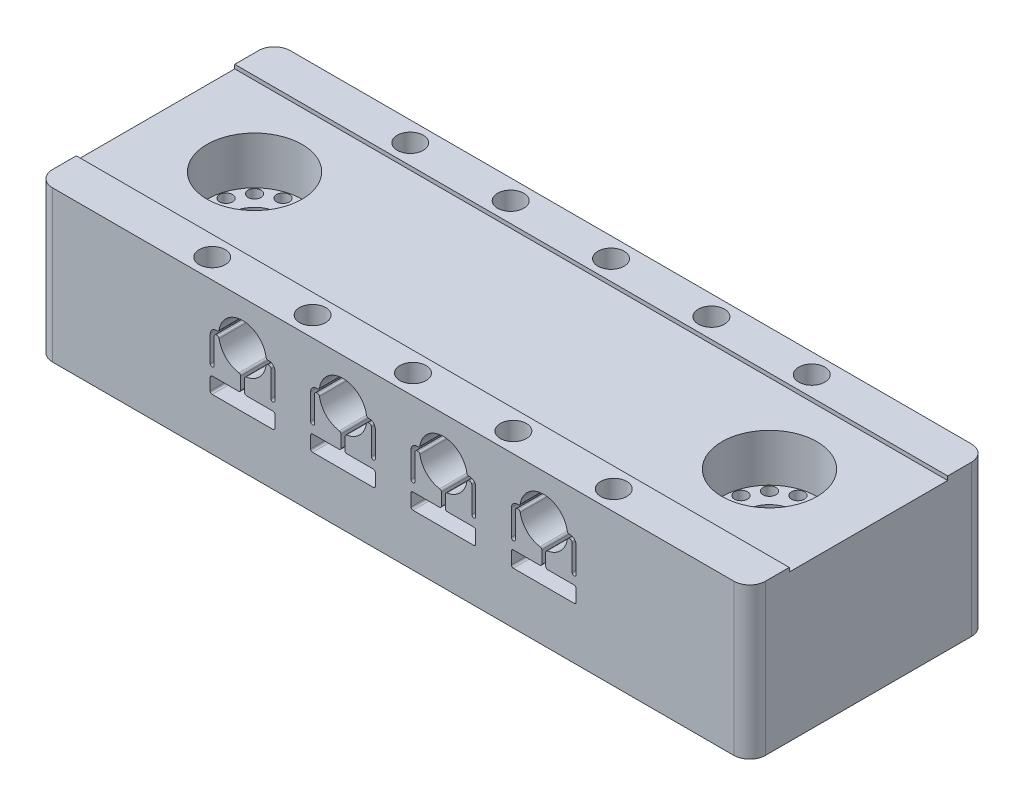
SolidWorks part; units mm, degrees
ref_plane "Front Plane" through (0, 0, 0) normal (0, 0, 1) x (1, 0, 0)
ref_plane "Top Plane" through (0, 0, 0) normal (0, 1, 0) x (1, 0, 0)
ref_plane "Right Plane" through (0, 0, 0) normal (1, 0, 0) x (0, 0, -1)
sketch "Sketch1" plane through (0, 0, 0) normal (0, 1, 0) x (1, 0, 0)
  line L0 (-45, 13) -> (-45, -13)
  line L3 (-43, -15) -> (43, -15)
  line L4 (45, -13) -> (45, 13)
  line L5 (43, 15) -> (-43, 15)
  line L6 (-32.5, 0) -> (32.5, 0) construction
  line L8 (-33.8159, 4.9109) -> (-36.095, 3.595) construction
  line L9 (-36.095, 3.595) -> (-37.4109, 1.3159) construction
  line L10 (-37.4109, 1.3159) -> (-37.4109, -1.3159) construction
  line L11 (-37.4109, -1.3159) -> (-36.095, -3.595) construction
  line L12 (-36.095, -3.595) -> (-33.8159, -4.9109) construction
  line L13 (-33.8159, -4.9109) -> (-31.1841, -4.9109) construction
  line L14 (-31.1841, -4.9109) -> (-28.905, -3.595) construction
  line L15 (-28.905, -3.595) -> (-27.5891, -1.3159) construction
  line L16 (-27.5891, -1.3159) -> (-27.5891, 1.3159) construction
  line L17 (-27.5891, 1.3159) -> (-28.905, 3.595) construction
  line L18 (-28.905, 3.595) -> (-31.1841, 4.9109) construction
  line L19 (-31.1841, 4.9109) -> (-33.8159, 4.9109) construction
  line L20 (33.8159, 4.9109) -> (31.1841, 4.9109) construction
  line L21 (31.1841, 4.9109) -> (28.905, 3.595) construction
  line L22 (28.905, 3.595) -> (27.5891, 1.3159) construction
  line L23 (27.5891, 1.3159) -> (27.5891, -1.3159) construction
  line L24 (27.5891, -1.3159) -> (28.905, -3.595) construction
  line L25 (28.905, -3.595) -> (31.1841, -4.9109) construction
  line L26 (31.1841, -4.9109) -> (33.8159, -4.9109) construction
  line L27 (33.8159, -4.9109) -> (36.095, -3.595) construction
  line L28 (36.095, -3.595) -> (37.4109, -1.3159) construction
  line L29 (37.4109, -1.3159) -> (37.4109, 1.3159) construction
  line L30 (37.4109, 1.3159) -> (36.095, 3.595) construction
  line L31 (36.095, 3.595) -> (33.8159, 4.9109) construction
  circle A2 centre (-32.5, 0) radius 3
  circle A3 centre (32.5, 0) radius 3
  circle A17 centre (32.5, 0) radius 6 construction
  circle A18 centre (-32.5, 0) radius 6 construction
  circle A19 centre (-31.1841, 4.9109) radius 0.9159 construction
  circle A20 centre (-31.1841, 4.9109) radius 0.8159
  circle A21 centre (-32.5, 0) radius 4.9109 construction
  circle A22 centre (-33.8159, 4.9109) radius 0.8159
  circle A23 centre (-33.8159, 4.9109) radius 1.8159 construction
  circle A24 centre (-36.095, 3.595) radius 0.8159
  circle A25 centre (-37.4109, 1.3159) radius 0.8159
  circle A26 centre (-37.4109, -1.3159) radius 0.8159
  circle A27 centre (-36.095, -3.595) radius 0.8159
  circle A28 centre (-33.8159, -4.9109) radius 0.8159
  circle A29 centre (-31.1841, -4.9109) radius 0.8159
  circle A30 centre (-28.905, -3.595) radius 0.8159
  circle A31 centre (-27.5891, -1.3159) radius 0.8159
  circle A32 centre (-27.5891, 1.3159) radius 0.8159
  circle A33 centre (-28.905, 3.595) radius 0.8159
  circle A34 centre (32.5, 0) radius 4.9109 construction
  circle A35 centre (31.1841, 4.9109) radius 0.8159
  circle A36 centre (33.8159, 4.9109) radius 0.8159
  circle A37 centre (36.095, 3.595) radius 0.8159
  circle A38 centre (37.4109, 1.3159) radius 0.8159
  circle A39 centre (37.4109, -1.3159) radius 0.8159
  circle A40 centre (36.095, -3.595) radius 0.8159
  circle A41 centre (33.8159, -4.9109) radius 0.8159
  circle A42 centre (31.1841, -4.9109) radius 0.8159
  circle A43 centre (28.905, -3.595) radius 0.8159
  circle A44 centre (27.5891, -1.3159) radius 0.8159
  circle A45 centre (27.5891, 1.3159) radius 0.8159
  circle A46 centre (28.905, 3.595) radius 0.8159
  arc A47 (43, -15) -> (45, -13) centre (43, -13) ccw
  arc A48 (-45, -13) -> (-43, -15) centre (-43, -13) ccw
  arc A49 (-45, 13) -> (-43, 15) centre (-43, 13) cw
  arc A50 (45, 13) -> (43, 15) centre (43, 13) ccw
  point P2 (-45, 0)
  point P6 (0, 15)
  point P72 (-45, 15)
  point P75 (45, 15)
  dimension "D1" = 90
  dimension "D2" = 12
  dimension "D3" = 65
  dimension "D4" = 6
  dimension "D5" = 30
  dimension "D6" = 0.1
  dimension "D7" = 1.6317
  dimension "D8" = 1
  dimension "D9" = 2
extrude "Boss-Extrude1" add sketch "Sketch1" along normal blind 19.05
sketch "Sketch2" plane through (0, 19.05, 0) normal (0, 1, 0) x (1, 0, 0)
  circle A0 centre (32.5, 0) radius 6 construction
  circle A1 centre (-32.5, 0) radius 6 construction
  circle A2 centre (32.5, 0) radius 6
  circle A3 centre (-32.5, 0) radius 6
extrude "Cut-Extrude1" cut sketch "Sketch2" against normal blind 6.5
sketch "Sketch3" plane through (0, 0, 15) normal (0, 0, 1) x (1, 0, 0)
  line L0 (0, 19.05) -> (0, 13.55) construction
  line L1 (-43, 19.05) -> (43, 19.05) construction
  line L2 (-22.2184, 13.8) -> (-22.3427, 13.8)
  line L3 (-22.2184, 13.3) -> (-22.3427, 13.3)
  line L4 (-23.0927, 13.05) -> (-23.0927, 9.8)
  line L5 (-22.5927, 13.05) -> (-22.5927, 9.8)
  line L6 (-15.7957, 13.8) -> (-15.6714, 13.8)
  line L7 (-15.7957, 13.3) -> (-15.6714, 13.3)
  line L8 (-15.4214, 13.05) -> (-15.4214, 9.8)
  line L9 (-14.9214, 13.05) -> (-14.9214, 9.8)
  line L10 (-19.257, 10.3387) -> (-19.257, 8.8)
  line L11 (-19.507, 8.55) -> (-22.8427, 8.55)
  line L12 (-18.757, 10.3387) -> (-18.757, 8.8)
  line L13 (-18.507, 8.55) -> (-15.1714, 8.55)
  line L14 (-22.8427, 6.5478) -> (-15.1714, 6.5478)
  line L15 (-23.0927, 8.3) -> (-23.0927, 6.7978)
  line L16 (-14.9214, 8.3) -> (-14.9214, 6.7978)
  line L17 (-19.007, 16.55) -> (-19.007, 19.05) construction
  line L18 (-22.2184, 13.3) -> (-22.2184, 13.8) construction
  line L19 (-22.8427, 9.55) -> (-22.8427, 8.55) construction
  line L20 (-19.257, 10.3387) -> (-18.757, 10.3387) construction
  line L21 (-21.507, 6.5478) -> (-21.507, 0) construction
  line L22 (-43, 0) -> (43, 0) construction
  line L23 (-16.507, 6.5478) -> (-16.507, 0) construction
  line L24 (-21.507, 3.2739) -> (-16.507, 3.2739) construction
  line L25 (-19.007, 3.2739) -> (-19.007, 6.5478) construction
  line L26 (-19.007, 8.55) -> (-19.007, 10.55) construction
  line L27 (-21.507, 6.5478) -> (-19.007, 8.05) construction
  line L28 (-19.007, 8.05) -> (-16.507, 6.5478) construction
  line L29 (-19.007, 13.55) -> (-14.9214, 13.55) construction
  line L30 (-14.9214, 13.55) -> (-10.4214, 13.55) construction
  line L31 (-10.4214, 13.55) -> (-6.3357, 13.55) construction
  line L32 (-6.3357, 13.55) -> (-2.25, 13.55) construction
  line L33 (-2.25, 13.55) -> (2.25, 13.55) construction
  line L34 (2.25, 13.55) -> (6.3357, 13.55) construction
  line L35 (6.3357, 13.55) -> (10.4214, 13.55) construction
  line L36 (10.4214, 13.55) -> (14.9214, 13.55) construction
  line L37 (14.9214, 13.55) -> (19.007, 13.55) construction
  arc A0 (-21.9713, 13.0885) -> (-19.4686, 10.5857) centre (-19.007, 13.55) ccw
  arc A1 (-22.3427, 13.8) -> (-23.0927, 13.05) centre (-22.3427, 13.05) ccw
  arc A2 (-22.3427, 13.3) -> (-22.5927, 13.05) centre (-22.3427, 13.05) ccw
  arc A3 (-23.0927, 9.8) -> (-22.5927, 9.8) centre (-22.8427, 9.8) ccw
  arc A4 (-15.6714, 13.8) -> (-14.9214, 13.05) centre (-15.6714, 13.05) cw
  arc A5 (-15.6714, 13.3) -> (-15.4214, 13.05) centre (-15.6714, 13.05) cw
  arc A6 (-15.4214, 9.8) -> (-14.9214, 9.8) centre (-15.1714, 9.8) ccw
  arc A7 (-16.0428, 14.0115) -> (-21.9713, 14.0115) centre (-19.007, 13.55) ccw
  arc A8 (-15.7957, 13.8) -> (-16.0428, 14.0115) centre (-15.7957, 14.05) cw
  arc A9 (-15.7957, 13.3) -> (-16.0428, 13.0885) centre (-15.7957, 13.05) ccw
  arc A10 (-22.2184, 13.3) -> (-21.9713, 13.0885) centre (-22.2184, 13.05) cw
  arc A11 (-22.2184, 13.8) -> (-21.9713, 14.0115) centre (-22.2184, 14.05) ccw
  arc A12 (-18.5455, 10.5857) -> (-16.0428, 13.0885) centre (-19.007, 13.55) ccw
  arc A13 (-19.257, 8.8) -> (-19.507, 8.55) centre (-19.507, 8.8) cw
  arc A14 (-22.8427, 8.55) -> (-23.0927, 8.3) centre (-22.8427, 8.3) ccw
  arc A15 (-23.0927, 6.7978) -> (-22.8427, 6.5478) centre (-22.8427, 6.7978) ccw
  arc A16 (-14.9214, 6.7978) -> (-15.1714, 6.5478) centre (-15.1714, 6.7978) cw
  arc A17 (-15.1714, 8.55) -> (-14.9214, 8.3) centre (-15.1714, 8.3) cw
  arc A18 (-18.757, 8.8) -> (-18.507, 8.55) centre (-18.507, 8.8) ccw
  arc A19 (-18.757, 10.3387) -> (-18.5455, 10.5857) centre (-18.507, 10.3387) cw
  arc A20 (-19.257, 10.3387) -> (-19.4686, 10.5857) centre (-19.507, 10.3387) ccw
  point P30 (-16.0175, 13.8)
  point P59 (-18.757, 10.5604)
  point P87 (0, 0)
  dimension "D1" = 2.5
  dimension "D2" = 1
  dimension "D5" = 3
  dimension "D3" = 0.5
  dimension "D4" = 5
  dimension "D6" = 2
  dimension "D7" = 118
  dimension "D8" = 0.5
  dimension "D9" = 4.0857
  dimension "D10" = 4.5
extrude "Cut-Extrude2" cut sketch "Sketch3" against normal through all
pattern_linear "LPattern1" count 4 spacing 12.6714 along (1, 0, 0) of "Cut-Extrude2"
sketch "Sketch4" plane through (0, 19.05, 0) normal (0, 1, 0) x (1, 0, 0)
  line L0 (-45, -10) -> (45, -10)
  line L1 (-45, 13) -> (-45, -13) construction
  line L2 (45, -13) -> (45, 13) construction
  line L3 (45, -10) -> (45, 10)
  line L4 (45, 10) -> (-45, 10)
  line L5 (-45, 10) -> (-45, -10)
  line L6 (10.4214, -15) -> (14.9214, -15) construction
  line L7 (-2.25, -15) -> (2.25, -15) construction
  line L8 (-14.9214, -15) -> (-10.4214, -15) construction
  line L9 (10.4214, -15) -> (14.9214, -15) construction
  line L10 (-2.25, -15) -> (2.25, -15) construction
  line L11 (-14.9214, -15) -> (-10.4214, -15) construction
  line L12 (-14.9214, -15) -> (-23.0927, -15) construction
  line L13 (-43, -15) -> (43, -15) construction
  line L14 (-23.0927, -15) -> (-27.5927, -15) construction
  line L15 (-10.4214, -15) -> (-2.25, -15) construction
  line L16 (-25.3427, -15) -> (-25.3427, -10) construction
  line L17 (-25.3427, 10) -> (-25.3427, 15) construction
  line L18 (43, 15) -> (-43, 15) construction
  line L20 (14.9214, -15) -> (23.0927, -15) construction
  line L21 (23.0927, -15) -> (27.5927, -15) construction
  line L22 (25.3427, -15) -> (25.3427, -10) construction
  circle A0 centre (-25.3427, -12.5) radius 2.5 construction
  circle A1 centre (-25.3427, -12.5) radius 2 construction
  circle A2 centre (-25.3427, 12.5) radius 2.5 construction
  circle A3 centre (-25.3427, 12.5) radius 2 construction
  point P9 (-45, 0)
  point P21 (25.3427, -12.5)
  dimension "D1" = 0.5
  dimension "D2" = 4
sketch "Sketch5" plane through (0, 19.05, 0) normal (0, 1, 0) x (1, 0, 0)
  point P0 (-25.3427, -12.5)
  point P3 (-25.3427, 12.5)
hole_wizard "M4x0.7 Tapped Hole1" positions "Sketch5" profile "Sketch6" tap size "M4x0.7" standard "ANSI Metric"
sketch "Sketch6" plane through (-25.3427, 19.05, 12.5) normal (1, 0, 0) x (0, 0, 1)
  line L0 (0, 0) -> (0, 11.0914)
  line L1 (0, 11.0914) -> (1.65, 10.1)
  line L2 (1.65, 10.1) -> (1.65, 0)
  line L5 (1.65, 0) -> (0, 0)
  line L10 (0, 11.0914) -> (-1.65, 10.1) construction
  line L11 (0, -6.35) -> (0, 107.95) construction
  dimension "Tap Drill Dia." = 3.3
  dimension "Tap Drill Depth" = 10.1
  dimension "Drill Angle" = 118
cosmetic thread "Hole Thread1" parameters "D1"=8, "D2"=4
cosmetic thread "Hole Thread2" parameters "D1"=8, "D2"=4
pattern_linear "LPattern2" count 5 spacing 12.6714 along (1, 0, 0) of "M4x0.7 Tapped Hole1"
cosmetic thread "Hole Thread3" parameters "D1"=8, "D2"=4
cosmetic thread "Hole Thread4" parameters "D1"=8, "D2"=4
cosmetic thread "Hole Thread5" parameters "D1"=8, "D2"=4
cosmetic thread "Hole Thread6" parameters "D1"=8, "D2"=4
cosmetic thread "Hole Thread7" parameters "D1"=8, "D2"=4
cosmetic thread "Hole Thread8" parameters "D1"=8, "D2"=4
cosmetic thread "Hole Thread9" parameters "D1"=8, "D2"=4
cosmetic thread "Hole Thread10" parameters "D1"=8, "D2"=4
extrude "Cut-Extrude3" cut sketch "Sketch4" against normal blind 0.5
sketch "Sketch7" plane through (0, 0, 0) normal (0, -1, 0) x (1, 0, 0)
  line L0 (-22.8427, 15) -> (-15.1714, 15) construction
  line L1 (-22.8427, 15) -> (-15.1714, 15) construction
  line L2 (15.1714, 15) -> (22.8427, 15) construction
  line L3 (15.1714, 15) -> (22.8427, 15) construction
  line L4 (-19.007, 5) -> (-19.007, -5) construction
  circle A0 centre (-19.007, 5) radius 2.5
  circle A1 centre (-19.007, -5) radius 2.5
  point P6 (-19.007, 15)
  point P7 (19.007, 15)
  point P8 (-19.007, 0)
  dimension "D2" = 5
  dimension "D1" = 10
extrude "Cut-Extrude4" cut sketch "Sketch7" against normal up to surface (6.5478 mm away)
pattern_linear "LPattern3" count 4 spacing 12.6714 along (1, 0, 0) of "Cut-Extrude4"
